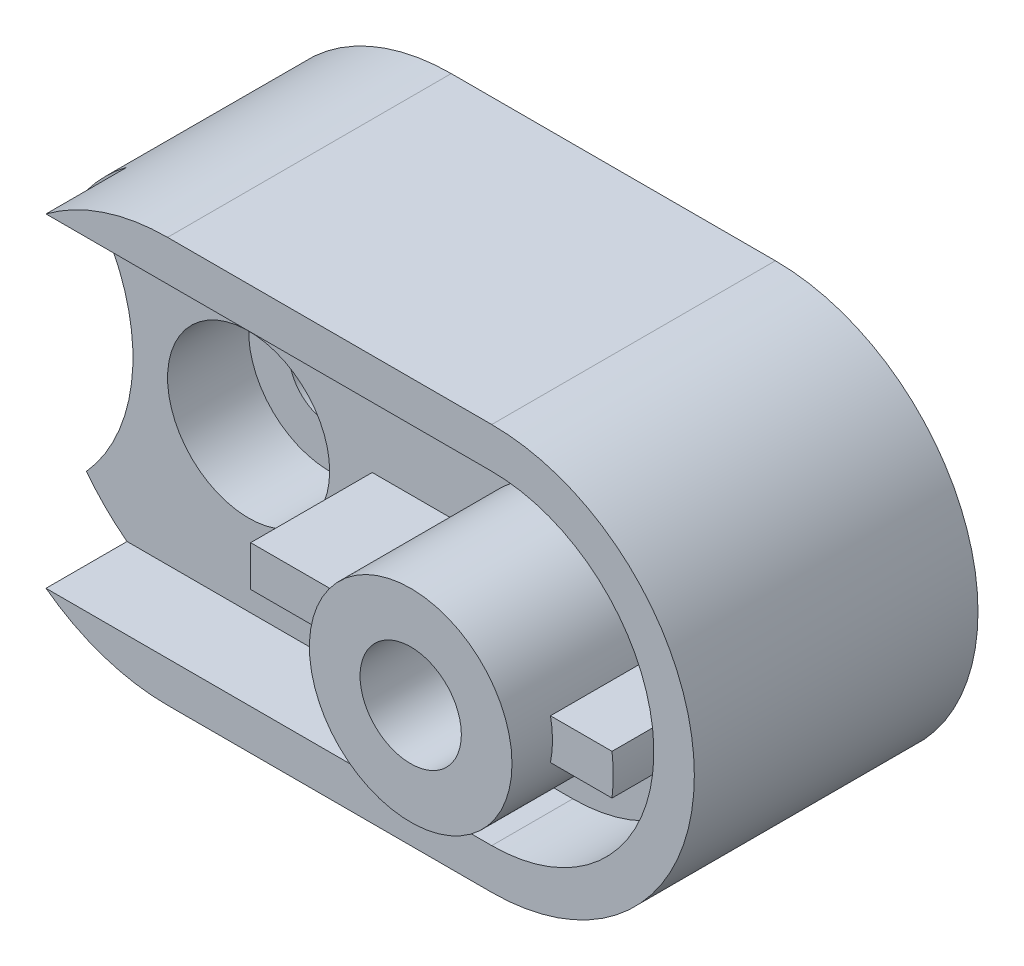
SolidWorks part; units mm, degrees
ref_plane "Front Plane" through (0, 0, 0) normal (0, 0, 1) x (1, 0, 0)
ref_plane "Top Plane" through (0, 0, 0) normal (0, 1, 0) x (1, 0, 0)
ref_plane "Right Plane" through (0, 0, 0) normal (1, 0, 0) x (0, 0, -1)
sketch "Sketch1" plane through (0, 0, 0) normal (0, 0, 1) x (1, 0, 0)
  line L1 (0, 0) -> (180, 0)
  line L2 (0, 0) -> (0, 100)
  line L3 (0, 100) -> (180, 100)
  line L4 (180, 0) -> (180, 100)
  dimension "D1" = 100
  dimension "D2" = 180
extrude "Boss-Extrude2" add sketch "Sketch1" along normal blind 70
sketch "Sketch2" plane through (0, 0, 70) normal (0, 0, 1) x (1, 0, 0)
  line L0 (180, 100) -> (0, 100) construction
  line L2 (180, 0) -> (180, 100) construction
  line L4 (0, 100) -> (180, 100)
  line L5 (0, 100) -> (0, 0)
  line L6 (0, 0) -> (180, 0)
  line L7 (180, 100) -> (180, 0)
  arc A0 (50, 100) -> (50, 0) centre (50, 50) ccw
  arc A1 (130, 100) -> (130, 0) centre (130, 50) cw
  line M1 (0, 100) -> (0, 0)
  line M2 (0, 0) -> (180, 0)
  line M3 (180, 0) -> (180, 100)
  line M4 (180, 100) -> (0, 100)
  dimension "D9" = 50
  dimension "D1" = 50
  dimension "D2" = 50
  dimension "D3" = 50
  dimension "D4" = 50
  dimension "D5" = 50
  dimension "D6" = 50
  dimension "D7" = 50
  dimension "D8" = 50
extrude "Cut-Extrude1" cut sketch "Sketch2" against normal blind 70 contours A0 L4 M1 | A0 L5 M2 | A1 M3 M2 | A1 L7 M4
sketch "Sketch3" plane through (0, 0, 70) normal (0, 0, 1) x (1, 0, 0)
  circle A0 centre (10, 50) radius 5
  arc A1 (50, 100) -> (50, 0) centre (50, 50) ccw construction
  point P2 (0, 50)
  dimension "D1" = 10
  dimension "D2" = 50
  dimension "D3" = 10
extrude "Cut-Extrude2" cut sketch "Sketch3" against normal blind 70
sketch "Sketch4" plane through (0, 0, 70) normal (0, 0, 1) x (1, 0, 0)
  arc A0 (10, 80) -> (10, 20) centre (-23.541, 50) cw
  arc A1 (50, 100) -> (50, 0) centre (50, 50) ccw construction
  arc A2 (10, 80) -> (10, 20) centre (50, 50) ccw
  circle M1 centre (10, 50) radius 5
  arc M4 (50, 100) -> (50, 0) centre (50, 50) ccw
  dimension "D1" = 40
  dimension "D5" = 45
  dimension "D2" = 40
  dimension "D3" = 20
  dimension "D4" = 20
extrude "Cut-Extrude3" cut sketch "Sketch4" against normal blind 50 contours A0 M4 M1
sketch "Sketch5" plane through (0, 0, 70) normal (0, 0, 1) x (1, 0, 0)
  circle A0 centre (50, 50) radius 10
  dimension "D1" = 20
extrude "Cut-Extrude4" cut sketch "Sketch5" against normal blind 106
sketch "Sketch6" plane through (0, 0, 70) normal (0, 0, 1) x (1, 0, 0)
  circle A0 centre (130, 50) radius 15
  dimension "D1" = 30
extrude "Cut-Extrude5" cut sketch "Sketch6" against normal blind 40
sketch "Sketch7" plane through (0, 0, 70) normal (0, 0, 1) x (1, 0, 0)
  point P0 (130, 50)
sketch "Sketch8" plane through (0, 0, 70) normal (0, 0, 1) x (1, 0, 0)
  circle A0 centre (130, 50) radius 15
  circle A1 centre (130, 50) radius 12.5
  dimension "D1" = 30
  dimension "D2" = 25
extrude "Boss-Extrude3" add sketch "Sketch8" against normal blind 40
sketch "Sketch10" plane through (0, 0, 70) normal (0, 0, 1) x (1, 0, 0)
  circle A0 centre (130, 50) radius 12.5
  dimension "D1" = 25
extrude "Boss-Extrude4" add sketch "Sketch10" against normal blind 65
hole_wizard "Ø25.0mm Dowel Hole2" positions "3DSketch2" profile "Sketch11" hole size "Ø25.0" standard "ISO"
sketch3d "3DSketch2"
  point P0 (130, 50, 70)
sketch "Sketch11" plane through (130, 50, 70) normal (1, 0, 0) x (0, -1, 0)
  line L0 (0, 0) -> (0, 27.5108)
  line L1 (0, 27.5108) -> (12.5, 20)
  line L2 (12.5, 20) -> (12.5, 0)
  line L5 (12.5, 0) -> (0, 0)
  line L10 (0, 27.5108) -> (-12.5, 20) construction
  line L11 (0, -6.35) -> (0, 107.95) construction
  dimension "Hole Dia." = 25
  dimension "Hole Depth" = 20
  dimension "Drill Angle" = 118
sketch "Sketch12" plane through (0, 0, 70) normal (0, 0, 1) x (1, 0, 0)
  line L0 (130, 90) -> (20, 90)
  line L2 (130, 10) -> (20, 10)
  line L3 (130, 100) -> (50, 100) construction
  line L4 (50, 100) -> (130, 100)
  line L5 (50, 0) -> (130, 0) construction
  line L6 (130, 0) -> (50, 0)
  arc A0 (130, 90) -> (130, 10) centre (130, 50) cw
  arc A3 (10, 80) -> (10, 20) centre (50, 50) ccw construction
  arc A4 (10, 20) -> (50, 0) centre (50, 50) ccw construction
  arc A5 (20, 90) -> (50, 100) centre (50, 50) cw
  arc A6 (130, 100) -> (130, 0) centre (130, 50) cw
  arc A7 (20, 10) -> (50, 0) centre (50, 50) ccw
  point P4 (0, 50)
  circle M1 centre (130, 50) radius 12.5
  circle M2 centre (50, 50) radius 10
  arc M3 (10, 80) -> (10, 20) centre (-23.541, 50) cw
  arc M4 (10, 20) -> (50, 0) centre (50, 50) ccw
  arc M8 (50, 100) -> (10, 80) centre (50, 50) ccw
  dimension "D3" = 40
  dimension "D1" = 10
  dimension "D2" = 10
  dimension "D4" = 110
  dimension "D5" = 20
extrude "Cut-Extrude6" cut sketch "Sketch12" against normal blind 20 contours A0 L0 L2 M8 M3 M4 M2 M1
sketch "Sketch13" plane through (0, 0, 50) normal (0, 0, 1) x (1, 0, 0)
  circle A0 centre (130, 50) radius 12.5
  circle A1 centre (130, 50) radius 25
  dimension "D1" = 25
  dimension "D2" = 50
extrude "Boss-Extrude5" add sketch "Sketch13" along normal blind 40
sketch "Sketch14" plane through (0, 0, 50) normal (0, 0, 1) x (1, 0, 0)
  circle A0 centre (50, 50) radius 10
  circle A1 centre (50, 50) radius 20
  dimension "D1" = 20
  dimension "D2" = 40
extrude "Cut-Extrude7" cut sketch "Sketch14" against normal blind 20
sketch "Sketch15" plane through (0, 0, 50) normal (0, 0, 1) x (1, 0, 0)
  line L1 (105.5051, 55) -> (80.5051, 55)
  line L2 (105.5051, 55) -> (105.5051, 45)
  line L3 (105.5051, 45) -> (80.5051, 45)
  line L4 (80.5051, 55) -> (80.5051, 45)
  line L5 (154.4949, 55) -> (169.6863, 55)
  line L6 (154.4949, 55) -> (154.4949, 45)
  line L7 (154.4949, 45) -> (169.6863, 45)
  line L8 (169.6863, 55) -> (169.6863, 45)
  circle A0 centre (130, 50) radius 25 construction
  arc A1 (130, 10) -> (130, 90) centre (130, 50) ccw construction
  arc A3 (105.5051, 55) -> (105.5051, 45) centre (130, 50) ccw
  arc A4 (154.4949, 55) -> (154.4949, 45) centre (130, 50) cw
  circle M8 centre (130, 50) radius 25
  dimension "D1" = 10
  dimension "D2" = 10
  dimension "D3" = 45
  dimension "D4" = 45
  dimension "D5" = 25
extrude "Boss-Extrude10" add sketch "Sketch15" along normal blind 30 contours L2 M8 | L1 L4 L3 M8
sketch "Sketch16" plane through (0, 0, 50) normal (0, 0, 1) x (1, 0, 0)
  line L1 (154.4949, 55) -> (170, 55)
  line L2 (154.4949, 55) -> (154.4949, 45)
  line L3 (154.4949, 45) -> (170, 45)
  line L4 (170, 55) -> (170, 45)
  arc A0 (105.5051, 45) -> (105.5051, 55) centre (130, 50) ccw construction
  arc A1 (130, 10) -> (130, 90) centre (130, 50) ccw construction
  arc A2 (154.4949, 55) -> (154.4949, 45) centre (130, 50) cw
  arc A3 (170, 55) -> (170, 45) centre (130, 50) cw
  arc M1 (130, 10) -> (130, 90) centre (130, 50) ccw
  arc M10 (105.5051, 55) -> (105.5051, 45) centre (130, 50) cw
  dimension "D1" = 45
  dimension "D2" = 10
extrude "Boss-Extrude13" add sketch "Sketch16" along normal blind 30 contours L3 L1 M10 M1
